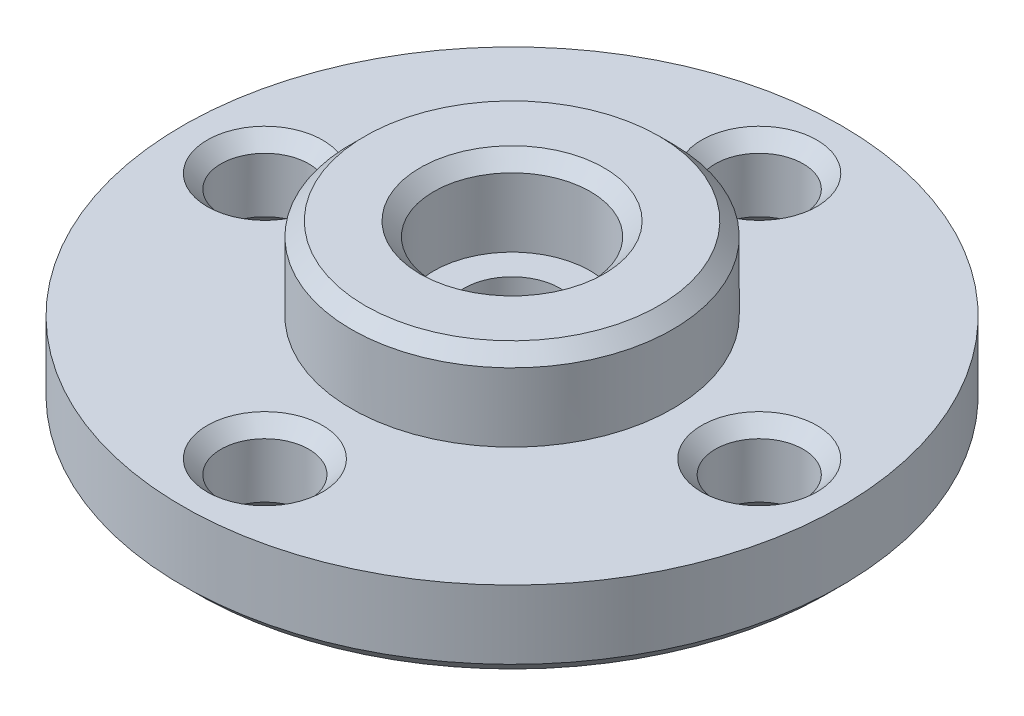
SolidWorks part; units mm, degrees
ref_plane "Front Plane" through (0, 0, 0) normal (0, 0, 1) x (1, 0, 0)
ref_plane "Top Plane" through (0, 0, 0) normal (0, 1, 0) x (1, 0, 0)
ref_plane "Right Plane" through (0, 0, 0) normal (1, 0, 0) x (0, 0, -1)
sketch "Sketch1" plane through (0, 0, 0) normal (0, 0, 1) x (1, 0, 0)
  line L0 (0, -26.626) -> (0, 38.2925) construction
  line L1 (1.75, 0) -> (1.75, 3)
  line L2 (1.75, 3) -> (2.85, 3)
  line L3 (2.85, 3) -> (2.85, 6)
  line L4 (2.85, 6) -> (5.85, 6)
  line L5 (5.85, 6) -> (5.85, 3)
  line L6 (5.85, 3) -> (12, 3)
  line L7 (12, 3) -> (12, 0)
  line L8 (12, 0) -> (1.75, 0)
  dimension "D1" = 3.5
  dimension "D2" = 5.7
  dimension "D3" = 24
  dimension "D4" = 3
  dimension "D5" = 3
  dimension "D6" = 11.7
revolve "Revolve1" add sketch "Sketch1" angle 360 about L0
sketch "Sketch2" plane through (0, 3, 0) normal (0, 1, 0) x (1, 0, 0)
  circle A0 centre (9, 0) radius 1.6
  point P2 (0, 0)
  dimension "D1" = 3.2
  dimension "D2" = 9
extrude "Cut-Extrude1" cut sketch "Sketch2" against normal through all
pattern_circular "CirPattern1" count 4 over 360 about axis through (0, 0, 0) along (0, 1, 0) of "Cut-Extrude1"
chamfer "Chamfer1" distance 0.5 angle 45 12 edges at (0, 0, -1.75) (0, 0, -12) (9, 0, 1.6) (-1.6, 0, 9) (-9, 0, -1.6) (1.6, 0, -9) (-1.6, 3, 9) (-9, 3, -1.6) (1.6, 3, -9) (9, 3, 1.6) (0, 6, -2.85) (0, 6, -5.85)
